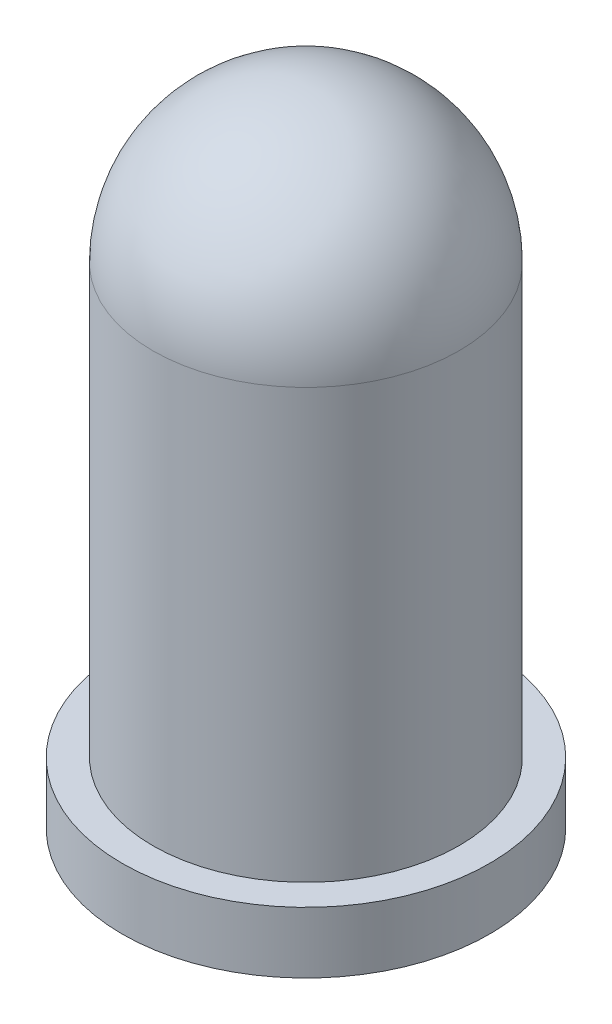
SolidWorks part; units mm, degrees
ref_plane "Front Plane" through (0, 0, 0) normal (0, 0, 1) x (1, 0, 0)
ref_plane "Top Plane" through (0, 0, 0) normal (0, 1, 0) x (1, 0, 0)
ref_plane "Right Plane" through (0, 0, 0) normal (1, 0, 0) x (0, 0, -1)
sketch "Sketch2" plane through (0, 0, 0) normal (0, 0, 1) x (1, 0, 0)
  line L0 (-2.5, 1) -> (-2.5, 8)
  line L1 (-3, 1) -> (-2.5, 1)
  line L2 (-3, 1) -> (-3, 0)
  line L3 (-3, 0) -> (3, 0)
  line L4 (3, 1) -> (3, 0)
  line L5 (2.5, 1) -> (3, 1)
  line L6 (2.5, 8) -> (2.5, 1)
  line L7 (0, 12.9063) -> (0, -7.9928) construction
  arc A0 (2.5, 8) -> (-2.5, 8) centre (0, 8) ccw
  point P12 (0, 0)
  dimension "D4" = 1
  dimension "D2" = 2.5
  dimension "D1" = 7
  dimension "D3" = 6
revolve "Revolve4" add sketch "Sketch2" angle 360 about L7
